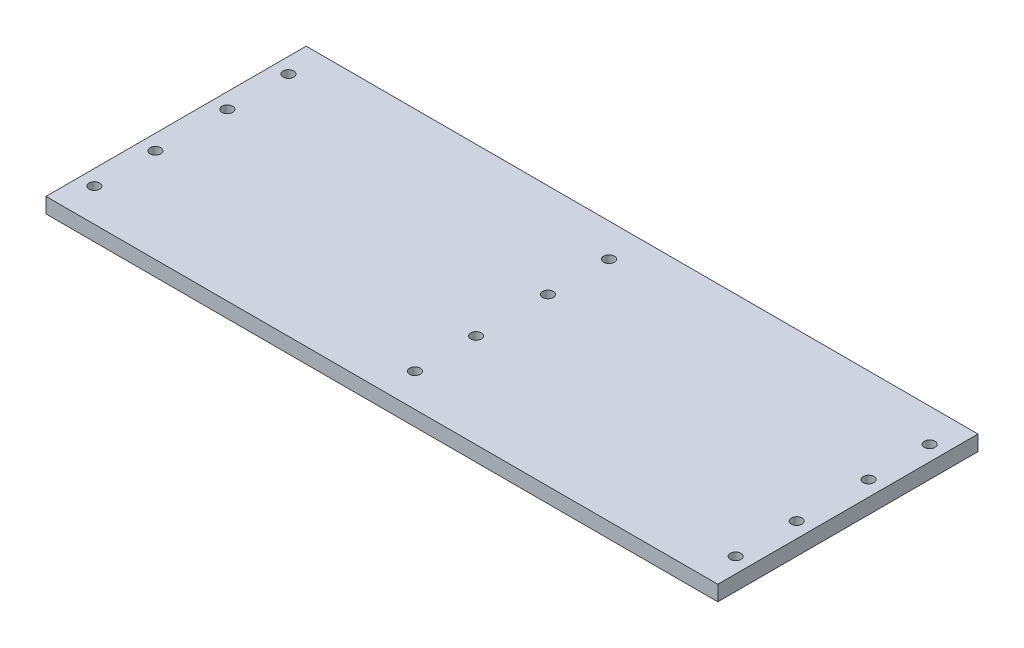
SolidWorks part; units mm, degrees
ref_plane "前视基准面" through (0, 0, 0) normal (0, 0, 1) x (1, 0, 0)
ref_plane "上视基准面" through (0, 0, 0) normal (0, 1, 0) x (1, 0, 0)
ref_plane "右视基准面" through (0, 0, 0) normal (1, 0, 0) x (0, 0, -1)
sketch "草图1" plane through (0, 0, 0) normal (0, 1, 0) x (1, 0, 0)
  line L1 (-65.705, 44.3173) -> (154.295, 44.3173)
  line L2 (-65.705, 44.3173) -> (-65.705, -40.8827)
  line L3 (-65.705, -40.8827) -> (154.295, -40.8827)
  line L4 (154.295, 44.3173) -> (154.295, -40.8827)
  dimension "D1" = 85.2
  dimension "D2" = 220
extrude "凸台-拉伸1" add sketch "草图1" along normal blind 5
sketch "草图2" plane through (0, 5, 0) normal (0, 1, 0) x (1, 0, 0)
  line L0 (-65.705, -40.8827) -> (154.295, -40.8827) construction
  line L1 (154.295, -40.8827) -> (154.295, 44.3173) construction
  line L2 (-65.705, 1.7173) -> (154.295, 1.7173)
  line L3 (-65.705, 44.3173) -> (-65.705, -40.8827) construction
  circle A0 centre (149.295, -30.0527) radius 1.75
  circle A1 centre (44.295, -30.0527) radius 1.75
  circle A2 centre (-60.705, -30.0527) radius 1.75
  circle A3 centre (44.295, -10.0527) radius 1.75
  circle A4 centre (-60.705, -10.0527) radius 1.75
  circle A5 centre (149.295, -10.0527) radius 1.75
  circle A6 centre (149.295, 13.4873) radius 1.75
  circle A7 centre (-60.705, 13.4873) radius 1.75
  circle A8 centre (44.295, 13.4873) radius 1.75
  circle A9 centre (-60.705, 33.4873) radius 1.75
  circle A10 centre (44.295, 33.4873) radius 1.75
  circle A11 centre (149.295, 33.4873) radius 1.75
  dimension "D2" = 5
  dimension "D3" = 3.5
  dimension "D1" = 10.83
  dimension "D4" = 3
  dimension "D5" = 2
extrude "切除-拉伸1" cut sketch "草图2" against normal blind 10 contours A0 | A5 | A3 | A1 | A8 | A10 | A6 | A11 | A9 | A7 | A4 | A2
